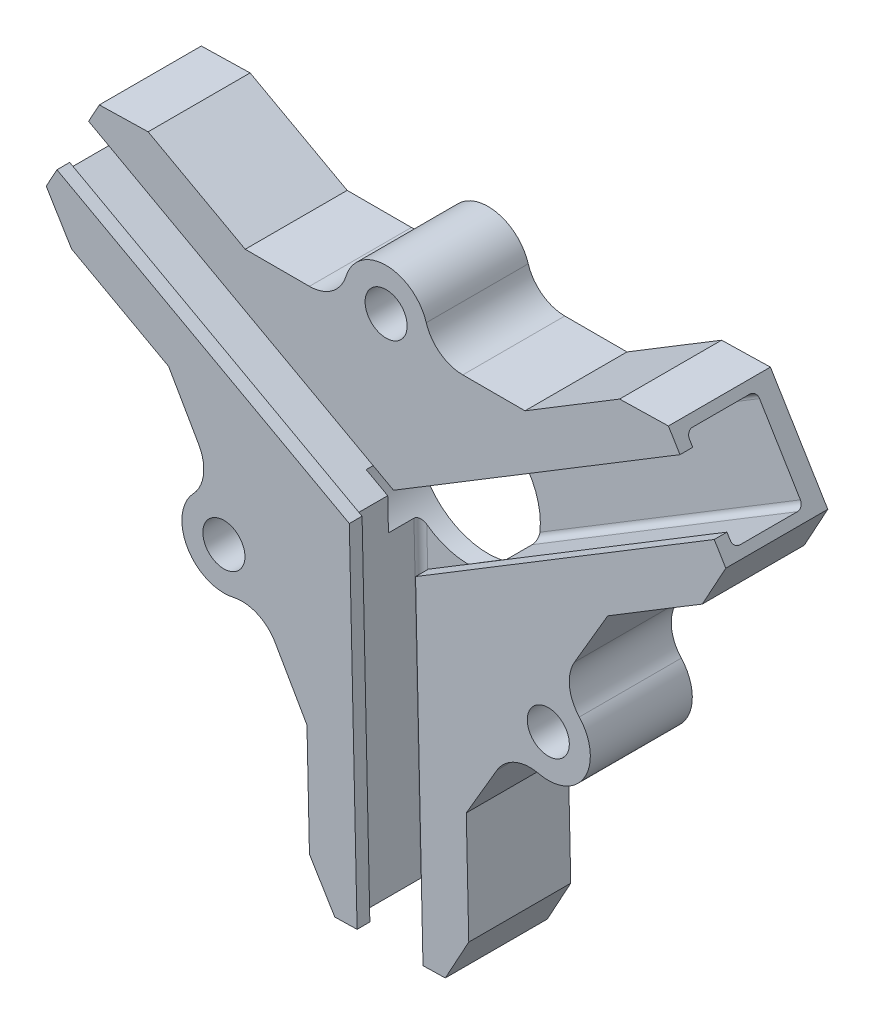
SolidWorks part; units mm, degrees
ref_plane "Front" through (0, 0, 0) normal (0, 0, 1) x (1, 0, 0)
ref_plane "Top" through (0, 0, 0) normal (0, 1, 0) x (1, 0, 0)
ref_plane "Right" through (0, 0, 0) normal (1, 0, 0) x (0, 0, -1)
sketch "Sketch1" plane through (0, 0, 0) normal (0, 0, 1) x (1, 0, 0)
  line L0 (12.2208, 14.8086) -> (5.2472, 10.5713) construction
  line L1 (5.7299, 25.4912) -> (-1.2437, 21.254) construction
  line L2 (-23.7771, 20.8993) -> (-31.3926, 25.0716)
  line L3 (-31.3926, 25.0716) -> (-35.2211, 24.9858)
  line L4 (-35.2211, 24.9858) -> (-39.3871, 17.3817)
  line L5 (-39.3871, 17.3817) -> (-37.3987, 14.109)
  line L6 (-37.3987, 14.109) -> (-29.7831, 9.9367)
  line L7 (-1.8275, 20.8993) -> (5.5936, 25.4084)
  line L8 (5.5936, 25.4084) -> (9.4221, 25.4941)
  line L9 (9.4221, 25.4941) -> (13.9244, 18.0841)
  line L10 (4.6633, 10.2166) -> (-6.4345, -8.7207)
  line L11 (-1.8275, 20.8993) -> (-23.7771, 20.8993)
  line L12 (-29.7831, 9.9367) -> (-18.9313, -9.0006)
  line L13 (-31.6587, 25.2174) -> (-24.5024, 21.2966) construction
  line L14 (-37.6647, 14.2548) -> (-30.5084, 10.3341) construction
  line L15 (13.9244, 18.0841) -> (12.0844, 14.7257)
  line L16 (12.0844, 14.7257) -> (4.6633, 10.2166)
  line L18 (-18.9313, -9.0006) -> (-18.7369, -17.682)
  line L19 (-18.7369, -17.682) -> (-16.7484, -20.9547)
  line L20 (-16.7484, -20.9547) -> (-8.08, -20.7606)
  line L21 (-8.08, -20.7606) -> (-6.24, -17.4021)
  line L22 (-24.3572, 0.468) -> (-1.8861, 13.3448) construction
  line L23 (-6.24, -17.4021) -> (-6.4345, -8.7207)
  line L24 (-12.8023, 20.8993) -> (-12.8023, 0.4606) construction
  line L25 (-0.8856, 0.748) -> (-21.1236, 12.608) construction
  arc A0 (-15.8185, 20.8993) -> (-9.6289, 20.8993) centre (-12.7237, 22.0381) cw
  arc A1 (-25.9561, 3.2583) -> (-22.8935, -2.0862) centre (-25.4474, 0) ccw
  arc A2 (0.5787, 3.2465) -> (-2.5496, -2.0915) centre (0, 0) cw
  circle A3 centre (0, 0) radius 1.125 construction
  circle A4 centre (-12.7237, 7.346) radius 2.5 construction
  circle A5 centre (-12.7237, 22.0381) radius 1.1727 construction
  circle A6 centre (-12.7237, 7.346) radius 2.565
  circle A7 centre (-25.4474, 0) radius 1.125 construction
  circle A13 centre (-12.7237, 22.0381) radius 1.65
  circle A16 centre (-25.4474, 0) radius 1.65
  circle A19 centre (0, 0) radius 1.65
  dimension "D9" = 3.2977
  dimension "D6" = 3.3
  dimension "D7" = 30
  dimension "D13" = 5.13
  dimension "D1" = 30
  dimension "D2" = 12
  dimension "D3" = 12
  dimension "D4" = 30
  dimension "D5" = 12
  dimension "D8" = 30
  dimension "D10" = 30
  dimension "D11" = 151.655
  dimension "D12" = 21.9495
extrude "Boss-Extrude2" add sketch "Sketch1" along normal blind 8 contours A19 L10 L16 L15 L9 L8 L7 L11 A13 L2 L3 L4 L5 L6 L12 A16 L18 L19 L20 L21 L23 | A13 L11 A0 | A19 L10 A2 | A16 L12 A1
sketch "Sketch2" plane through (18.1951, 11.0554, 0) normal (0.8546, 0.5193, 0) x (0, 0, -1)
  line L0 (-1.5, 8.9744) -> (-1.5, 16.145)
  line L1 (-1.5, 16.145) -> (-7, 16.145)
  line L2 (-7, 16.145) -> (-7, 15.145)
  line L3 (-7, 15.145) -> (-8, 15.145)
  line L4 (-8, 16.895) -> (-8, 8.2244) construction
  line L5 (-8, 15.145) -> (-8, 9.9744)
  line L6 (-8, 9.9744) -> (-7, 9.9744)
  line L7 (-7, 9.9744) -> (-7, 8.9744)
  line L8 (-7, 8.9744) -> (-1.5, 8.9744)
  line L11 (-8, 12.5597) -> (5, 12.5597) construction
  line L12 (0, 16.895) -> (0, 8.2244) construction
  line L13 (-8, 16.895) -> (0, 16.895) construction
  point P2 (-8, 12.5597)
  point P12 (-1.5, 12.5597)
  dimension "D1" = 1.5
  dimension "D2" = 0.75
  dimension "D3" = 1
  dimension "D4" = 1
extrude "Cut-Extrude1" cut sketch "Sketch2" against normal offset from surface (28.9379 mm away) 13
sketch "Sketch3" plane through (0.4607, -20.5693, 0) normal (0.0224, -0.9997, 0) x (0.9997, 0.0224, 0)
  line L0 (-16.4634, 1.5) -> (-9.2928, 1.5)
  line L1 (-9.2928, 1.5) -> (-9.2928, 7)
  line L2 (-9.2928, 7) -> (-10.2928, 7)
  line L3 (-10.2928, 7) -> (-10.2928, 8)
  line L4 (-17.2134, 8) -> (-8.5428, 8) construction
  line L5 (-10.2928, 8) -> (-15.4634, 8)
  line L6 (-15.4634, 8) -> (-15.4634, 7)
  line L7 (-15.4634, 7) -> (-16.4634, 7)
  line L8 (-16.4634, 7) -> (-16.4634, 1.5)
  line L9 (-17.2134, 0) -> (-8.5428, 0) construction
  line L10 (-12.8781, 8) -> (-12.8781, 0) construction
  line L11 (-17.2134, 8) -> (-17.2134, 0) construction
  dimension "D1" = 1.5
  dimension "D2" = 1
  dimension "D3" = 0.75
  dimension "D4" = 1
extrude "Cut-Extrude2" cut sketch "Sketch3" against normal offset from surface (28.822 mm away) 13
sketch "Sketch4" plane through (-37.6185, 20.6099, 0) normal (-0.877, 0.4805, 0) x (0, 0, 1)
  line L0 (1.5, 4.2396) -> (1.5, -2.931)
  line L1 (1.5, -2.931) -> (7, -2.931)
  line L2 (7, -2.931) -> (7, -1.931)
  line L3 (7, -1.931) -> (8, -1.931)
  line L4 (8, 4.9896) -> (8, -3.681) construction
  line L5 (8, -1.931) -> (8, 3.2396)
  line L6 (8, 3.2396) -> (7, 3.2396)
  line L7 (7, 3.2396) -> (7, 4.2396)
  line L8 (7, 4.2396) -> (1.5, 4.2396)
  line L9 (0, 4.9896) -> (0, -3.681) construction
  line L10 (0, 0.6543) -> (8, 0.6543) construction
  line L11 (8, 4.9896) -> (0, 4.9896) construction
  dimension "D1" = 1.5
  dimension "D2" = 0.75
  dimension "D3" = 1
  dimension "D4" = 1
extrude "Cut-Extrude3" cut sketch "Sketch4" against normal offset from surface (28.8398 mm away) 13
fillet "Fillet1" radius 3 6 edges at (-22.8935, -2.0862, 4) (-25.9561, 3.2583, 4) (-15.8185, 20.8993, 4) (-9.6289, 20.8993, 4) (0.5787, 3.2465, 4) (-2.5496, -2.0915, 4)
fillet "Fillet2" radius 0.5 12 edges at (-9.1161, -7.9946, 7) (-16.2975, -7.5937, 7) (-9.1161, -7.9946, 1.5) (-16.2975, -7.5937, 1.5) (-1.1772, 18.1763, 7) (2.0663, 11.7567, 7) (2.0663, 11.7567, 1.5) (-1.1772, 18.1763, 1.5) (-27.8116, 11.895, 7) (-23.8737, 17.9138, 7) (-23.8737, 17.9138, 1.5) (-27.8116, 11.895, 1.5)
sketch "Sketch5" plane through (0, 0, 0) normal (0, 0, -1) x (-1, 0, 0)
  circle A0 centre (12.7237, 7.346) radius 2.565 construction
  circle A1 centre (12.7237, 7.346) radius 2.565 construction
  circle A2 centre (12.7237, 7.346) radius 5.6
  dimension "D1" = 11.2
extrude "Cut-Extrude4" cut sketch "Sketch5" against normal blind 4
